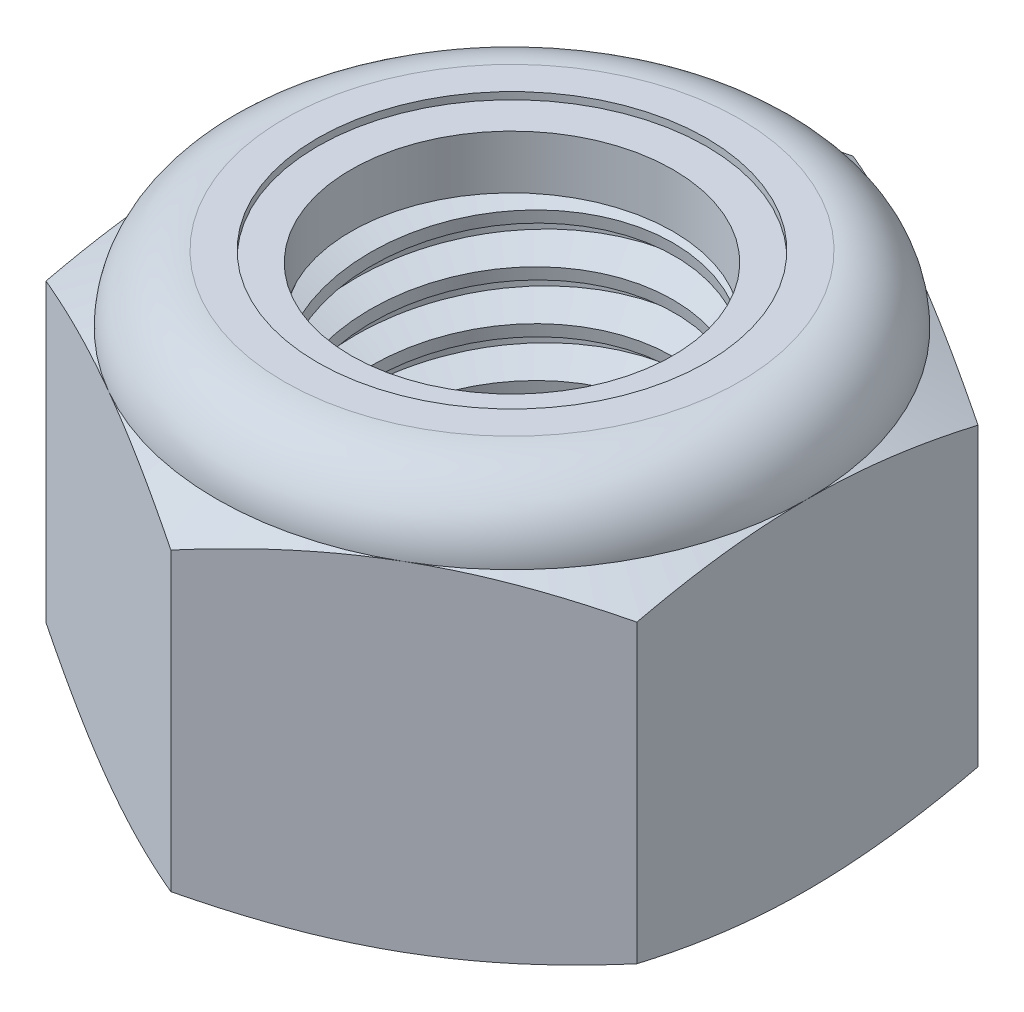
SolidWorks part; units mm, degrees
ref_plane "Front" through (0, 0, 0) normal (0, 0, 1) x (1, 0, 0)
ref_plane "Top" through (0, 0, 0) normal (0, 1, 0) x (1, 0, 0)
ref_plane "Right" through (0, 0, 0) normal (1, 0, 0) x (0, 0, -1)
sketch "Sketch1" plane through (0, 0, 0) normal (0, 1, 0) x (1, 0, 0)
  line L1 (0, 7.3323) -> (-6.35, 3.6662)
  line L2 (-6.35, 3.6662) -> (-6.35, -3.6662)
  line L3 (-6.35, -3.6662) -> (0, -7.3323)
  line L4 (0, -7.3323) -> (6.35, -3.6662)
  line L5 (6.35, -3.6662) -> (6.35, 3.6662)
  line L6 (6.35, 3.6662) -> (0, 7.3323)
  circle A0 centre (0, 0) radius 6.35 construction
  dimension "Hex Flats" = 12.7
extrude "Extrude1" add sketch "Sketch1" along normal blind 8.7312
sketch "Sketch2" plane through (0, 0, 0) normal (1, 0, 0) x (0, 0, -1)
  line L0 (-3.9688, 0) -> (-3.9688, 8.7312) construction
  line L1 (0, 0) -> (3.9688, 0)
  line L2 (0, 0) -> (0, 8.7312)
  line L3 (0, 8.7312) -> (3.9688, 8.7312)
  line L4 (3.9688, 0) -> (3.9688, 8.7312)
  line L5 (-3.6662, 8.7312) -> (3.6662, 8.7312) construction
  line L7 (0, -3.9688) -> (0, 0) construction
  dimension "Thread Dia" = 7.9375
revolve "Revolve1" add sketch "Sketch2" angle 360 about L7
sketch "Sketch3" plane through (0, 0, 0) normal (1, 0, 0) x (0, 0, -1)
  line L0 (3.9688, 8.7312) -> (-3.9688, 8.7312) construction
  line L1 (-3.9688, 8.7312) -> (-3.9688, 7.6729) construction
  line L2 (-3.9688, 7.6729) -> (3.9688, 8.7312) construction
  line L3 (3.9688, 8.7312) -> (3.9862, 8.6001) construction
  line L4 (3.9862, 8.6001) -> (4.1086, 7.6822)
  line L5 (4.1086, 7.6822) -> (3.4971, 7.9343)
  line L6 (3.4971, 7.9343) -> (3.4621, 8.1966)
  line L7 (3.4621, 8.1966) -> (3.9862, 8.6001)
  line L8 (3.4796, 8.0655) -> (4.0474, 8.1412) construction
  line L9 (3.9688, 8.7312) -> (3.9688, 8.1307) construction
  line L10 (3.9688, 8.1307) -> (-3.9688, 7.0723) construction
  line L11 (-3.9688, 7.0723) -> (-3.9688, 7.6729) construction
  line L12 (-0.1506, 8.7312) -> (0.1506, 6.4718) construction
  line L13 (-3.9688, 0) -> (-3.9688, 8.7312) construction
  line L14 (0, 8.7312) -> (3.9688, 8.7312) construction
  line L15 (3.9688, 0) -> (3.9688, 8.7312) construction
  point P13 (0, 7.6015)
  dimension "D1" = 0.1323
  dimension "D2" = 0.2646
  dimension "Thread Pitch" = 1.0583
  dimension "D4" = 60
  dimension "D5" = 1.0583
revolve "Cut-Revolve1" cut sketch "Sketch3" angle 360 about L12
pattern_linear "LPattern1" count 8 spacing 1.0583 along (0, -1, 0) count 2 spacing 1.0583 along (0, 1, 0) of "Cut-Revolve1"
sketch "Sketch4" plane through (0, 0, 0) normal (1, 0, 0) x (0, 0, -1)
  line L0 (0, 8.7312) -> (3.9688, 8.7312)
  line L1 (3.9688, 8.7312) -> (3.4621, 8.495)
  line L2 (3.4621, 8.495) -> (3.4621, 0.2362)
  line L3 (3.4621, 0.2362) -> (3.9688, 0)
  line L4 (3.9688, 0) -> (0, 0)
  line L5 (0, 0) -> (0, 8.7312)
  line L6 (3.9688, 0) -> (3.9688, 8.7312) construction
  line L7 (0, 8.7312) -> (3.9688, 8.7312) construction
  line L8 (0, 0) -> (3.9688, 0) construction
  line L9 (0, 0) -> (0, 8.7312) construction
  line L10 (0, 8.7312) -> (0, 9.2902) construction
  dimension "D1" = 25
revolve "Cut-Revolve2" cut sketch "Sketch4" angle 360 about L10
combine bodies "Combine1" operation type subtract main body 112 bodies to subtract 111
sketch "Sketch5" plane through (0, 0, 0) normal (1, 0, 0) x (0, 0, -1)
  line L0 (0, 0) -> (6.35, 0)
  line L1 (6.35, 0) -> (7.3323, 0.4581)
  line L2 (7.3323, 0.4581) -> (7.3323, 6.818)
  line L3 (7.3323, 6.818) -> (6.35, 7.276)
  line L4 (4.8948, 8.7312) -> (4.8948, 10.0012)
  line L5 (4.8948, 10.0012) -> (8.6023, 10.0012)
  line L6 (8.6023, 10.0012) -> (8.6023, -1.27)
  line L7 (8.6023, -1.27) -> (0, -1.27)
  line L8 (0, -1.27) -> (0, 0)
  line L9 (6.35, 7.276) -> (6.35, 0) construction
  line L10 (0, 0) -> (3.9688, 0) construction
  line L13 (7.3323, 3.638) -> (8.6023, 3.638) construction
  line L14 (7.3323, 8.7312) -> (7.3323, 0) construction
  line L15 (0, 0) -> (0, 10.0012) construction
  line L20 (0, 10.0012) -> (4.8948, 10.0012) construction
  line L22 (0, 8.7312) -> (3.9688, 8.7312) construction
  arc A0 (6.35, 7.276) -> (4.8948, 8.7312) centre (4.8948, 7.276) ccw
  dimension "D1" = 25
  dimension "D2" = 1.27
  dimension "D3" = 8.7312
  dimension "D4" = 1.4552
revolve "Cut-Revolve3" cut sketch "Sketch5" angle 360 about L15
sketch "Sketch6" plane through (0, 0, 0) normal (1, 0, 0) x (0, 0, -1)
  line L0 (0, 7.276) -> (6.1976, 7.276)
  line L1 (4.8948, 8.5788) -> (4.1785, 8.5788)
  line L2 (0, 10.0012) -> (0, 7.276)
  line L3 (4.1785, 10.0012) -> (0, 10.0012)
  line L4 (0, 10.0012) -> (4.8948, 10.0012) construction
  line L5 (0, 0) -> (0, 10.0012) construction
  line L6 (0, 10.0012) -> (0, 44.323) construction
  line L7 (4.1785, 8.5788) -> (4.1785, 10.0012)
  line L8 (4.8948, 8.7312) -> (4.8948, 8.5788) construction
  line L9 (4.1785, 8.5788) -> (3.4621, 8.5788) construction
  line L10 (3.4621, 8.5788) -> (3.4621, 8.495) construction
  arc A0 (6.1976, 7.276) -> (4.8948, 8.5788) centre (4.8948, 7.276) ccw
  arc A1 (6.35, 7.276) -> (4.8948, 8.7312) centre (4.8948, 7.276) ccw construction
  dimension "D1" = 0.1524
revolve "Cut-Revolve4" cut sketch "Sketch6" angle 360 about L6
sketch "Sketch7" plane through (0, 0, 0) normal (1, 0, 0) x (0, 0, -1)
  line L0 (3.4621, 7.3522) -> (6.119, 7.3522)
  line L1 (4.8948, 8.5026) -> (3.4621, 8.5026)
  line L2 (3.4621, 8.5026) -> (3.4621, 7.3522)
  line L3 (3.4621, 7.3522) -> (0, 7.3522) construction
  line L4 (0, 7.3522) -> (0, 8.5026) construction
  line L5 (0, 8.5026) -> (3.4621, 8.5026) construction
  line L6 (3.4621, 7.3522) -> (3.4621, 7.276) construction
  line L7 (0, 7.276) -> (6.1976, 7.276) construction
  line L8 (4.8948, 8.5026) -> (4.8948, 8.5788) construction
  arc A0 (6.119, 7.3522) -> (4.8948, 8.5026) centre (4.8948, 7.276) ccw
  arc A2 (6.1976, 7.276) -> (4.8948, 8.5788) centre (4.8948, 7.276) ccw construction
  dimension "D1" = 0.0762
revolve "Revolve2" add sketch "Sketch7" angle 360 about L4
equation "\"D1@Sketch3\"=\"Thread Pitch@Sketch3\"/8"
equation "\"D2@Sketch3\"=\"Thread Pitch@Sketch3\"/4"
equation "\"D5@Sketch3\"=\"Thread Pitch@Sketch3\""
equation "\"D4@LPattern1\"=\"Thread Pitch@Sketch3\""
equation "\"D3@LPattern1\"=\"Thread Pitch@Sketch3\""
equation "\"D1@LPattern1\"=\"Height@Extrude1\"/\"Thread Pitch@Sketch3\""
equation "\"D4@Sketch5\"=\"Height@Extrude1\"/6"
